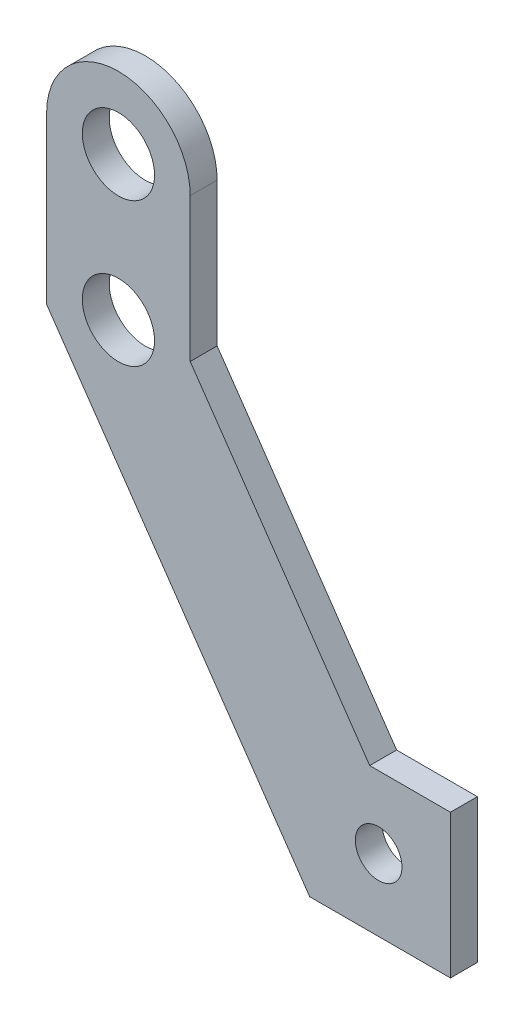
SolidWorks part; units mm, degrees
ref_plane "正面" through (0, 0, 0) normal (0, 0, 1) x (1, 0, 0)
ref_plane "平面" through (0, 0, 0) normal (0, 1, 0) x (1, 0, 0)
ref_plane "右側面" through (0, 0, 0) normal (1, 0, 0) x (0, 0, -1)
sketch "ｽｹｯﾁ1" plane through (0, 0, 0) normal (0, 0, 1) x (1, 0, 0)
  line L3 (0, 46) -> (0, 0) construction
  line L4 (16, 30) -> (16, 46) construction
  line L8 (0, 46) -> (0, 27.5089)
  line L9 (16, 30) -> (16, 46)
  line L10 (16, 30) -> (36, 1) construction
  line L11 (45, 1) -> (36, 1) construction
  line L12 (45, -15) -> (45, 1) construction
  line L13 (29.3165, -15) -> (45, -15) construction
  line L14 (0, 27.5089) -> (29.3165, -15) construction
  line L15 (16, 30) -> (36, 1)
  line L16 (45, 1) -> (36, 1)
  line L17 (45, -15) -> (45, 1)
  line L18 (29.3165, -15) -> (45, -15)
  line L19 (0, 27.5089) -> (29.3165, -15)
  arc A2 (16, 46) -> (0, 46) centre (8, 46) ccw construction
  circle A3 centre (8, 30) radius 4.025
  circle A4 centre (8, 46) radius 4.025
  arc A5 (16, 46) -> (0, 46) centre (8, 46) ccw
  circle A6 centre (37, -7) radius 2.6 construction
  circle A7 centre (37, -7) radius 2.6
  dimension "D1" = 8.05
  dimension "D2" = 8.05
extrude "ﾎﾞｽ - 押し出し1" add sketch "ｽｹｯﾁ1" along normal blind 3 from surface at 10
